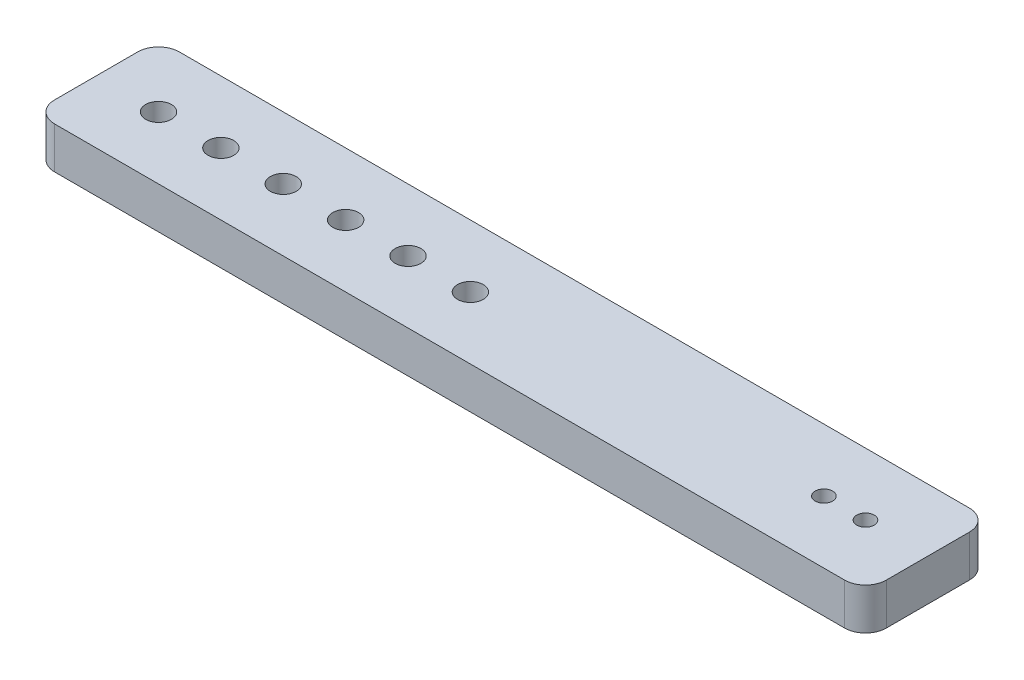
SolidWorks part; units mm, degrees
ref_plane "Front Plane" through (0, 0, 0) normal (0, 0, 1) x (1, 0, 0)
ref_plane "Top Plane" through (0, 0, 0) normal (0, 1, 0) x (1, 0, 0)
ref_plane "Right Plane" through (0, 0, 0) normal (1, 0, 0) x (0, 0, -1)
sketch "Sketch1" plane through (0, 0, 0) normal (0, 1, 0) x (1, 0, 0)
  line L1 (100, -15) -> (-100, -15)
  line L2 (100, -15) -> (100, 15)
  line L3 (100, 15) -> (-100, 15)
  line L4 (-100, -15) -> (-100, 15)
  line L5 (0, 15) -> (0, -15) construction
  line L6 (100, 0) -> (-100, 0) construction
  point P0 (0, 0)
  dimension "D1" = 200
  dimension "D2" = 30
extrude "Boss-Extrude1" add sketch "Sketch1" along normal blind 10
sketch "Sketch2" plane through (0, 10, 0) normal (0, 1, 0) x (1, 0, 0)
  line L0 (0, 0) -> (100, 0) construction
  line L1 (100, -15) -> (100, 15) construction
  circle A0 centre (85, 0) radius 2.1
  circle A1 centre (75, 0) radius 2.1
  dimension "D1" = 4.2
  dimension "D2" = 10
  dimension "D3" = 15
extrude "Cut-Extrude1" cut sketch "Sketch2" against normal through all
sketch "Sketch3" plane through (0, 10, 0) normal (0, 1, 0) x (1, 0, 0)
  line L0 (-100, 0) -> (100, 0) construction
  line L1 (-100, 15) -> (-100, -15) construction
  line L2 (100, -15) -> (100, 15) construction
  circle A0 centre (-85, 0) radius 3.1
  dimension "D1" = 6.2
  dimension "D2" = 15
extrude "Cut-Extrude2" cut sketch "Sketch3" against normal through all
pattern_linear "LPattern1" count 6 spacing 15 along (1, 0, 0) of "Cut-Extrude2"
fillet "Fillet1" radius 5 4 edges at (100, 5, -15) (100, 5, 15) (-100, 5, -15) (-100, 5, 15)
